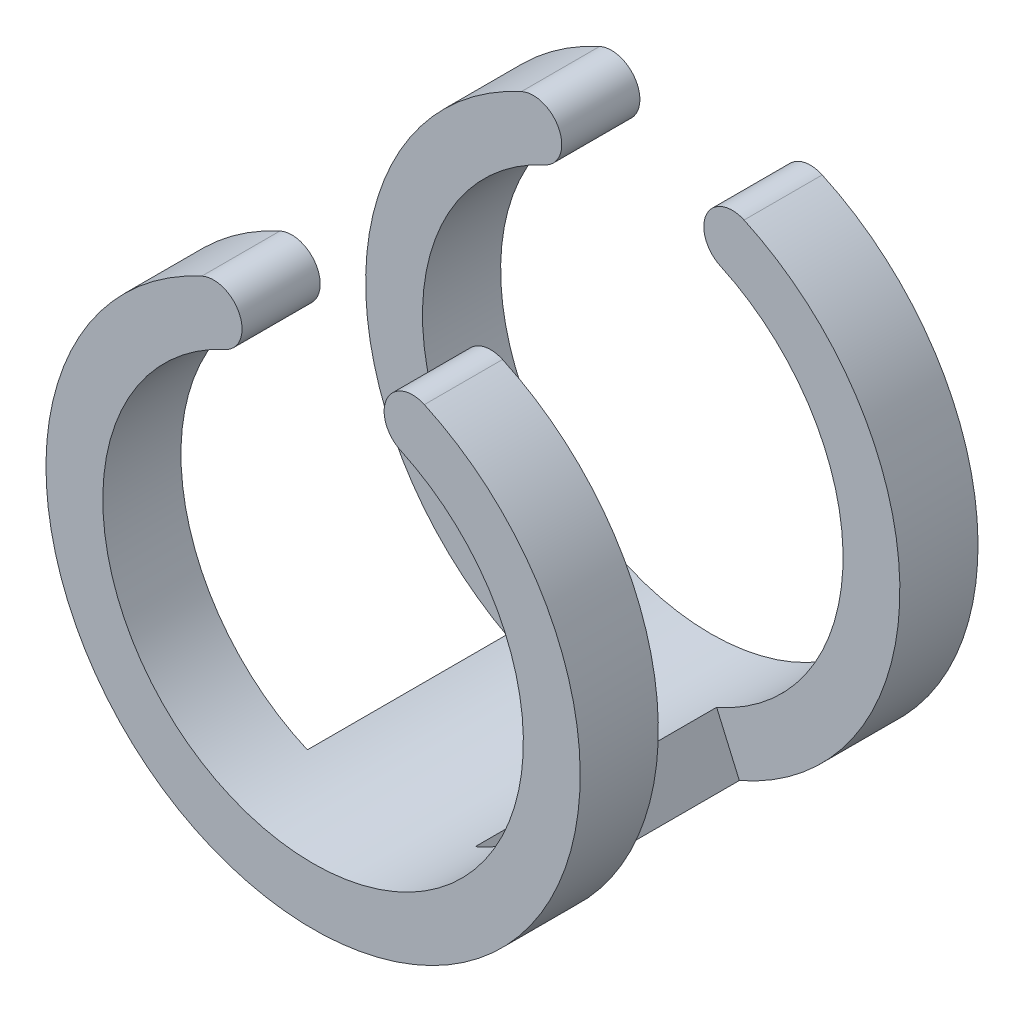
SolidWorks part; units mm, degrees
ref_plane "前视基准面" through (0, 0, 0) normal (0, 0, 1) x (1, 0, 0)
ref_plane "上视基准面" through (0, 0, 0) normal (0, 1, 0) x (1, 0, 0)
ref_plane "右视基准面" through (0, 0, 0) normal (1, 0, 0) x (0, 0, -1)
sketch "草图1" plane through (0, 0, 0) normal (0, 0, 1) x (1, 0, 0)
  line L0 (-3.9167, 8.5452) -> (0, 0) construction
  line L1 (0, 0) -> (3.9167, 8.5452) construction
  arc A0 (-3.0833, 6.727) -> (3.0833, 6.727) centre (0, 0) ccw
  arc A1 (-3.9167, 8.5452) -> (3.9167, 8.5452) centre (0, 0) ccw
  arc A2 (-3.9167, 8.5452) -> (-3.0833, 6.727) centre (-3.5, 7.6361) cw
  arc A3 (3.9167, 8.5452) -> (3.0833, 6.727) centre (3.5, 7.6361) ccw
  point P9 (2.2597, 6.8889)
  point P10 (-4.0004, 9.4371)
  dimension "D1" = 7.4
  dimension "D3" = 5
  dimension "D2" = 2
extrude "凸台-拉伸1" add sketch "草图1" along normal mid plane 14
sketch "草图2" plane through (0, 0, 0) normal (0, 0, 1) x (1, 0, 0)
  line L0 (0, 0) -> (-3.75, -8.6196) construction
  line L1 (0, 0) -> (3.75, -8.6196) construction
  line L2 (-2.9521, -6.7856) -> (-3.75, -8.6196)
  line L3 (2.9521, -6.7856) -> (3.75, -8.6196)
  arc A0 (2.9521, -6.7856) -> (3.0833, 6.727) centre (0, 0) ccw
  arc A1 (3.75, -8.6196) -> (3.9167, 8.5452) centre (0, 0) ccw
  arc A4 (-3.0833, 6.727) -> (-3.9167, 8.5452) centre (-3.5, 7.6361) ccw
  arc A5 (-3.9167, 8.5452) -> (3.9167, 8.5452) centre (0, 0) ccw
  arc A6 (3.9167, 8.5452) -> (3.0833, 6.727) centre (3.5, 7.6361) ccw
  arc A7 (-3.0833, 6.727) -> (3.0833, 6.727) centre (0, 0) ccw
  arc A8 (-3.0833, 6.727) -> (-3.9167, 8.5452) centre (-3.5, 7.6361) ccw
  arc A9 (-3.9167, 8.5452) -> (-3.75, -8.6196) centre (0, 0) ccw
  arc A10 (3.9167, 8.5452) -> (3.0833, 6.727) centre (3.5, 7.6361) ccw
  arc A11 (-3.0833, 6.727) -> (-2.9521, -6.7856) centre (0, 0) ccw
  dimension "D2" = 7.5
  dimension "D1" = 0
extrude "切除-拉伸1" cut sketch "草图2" against normal mid plane 8.5
